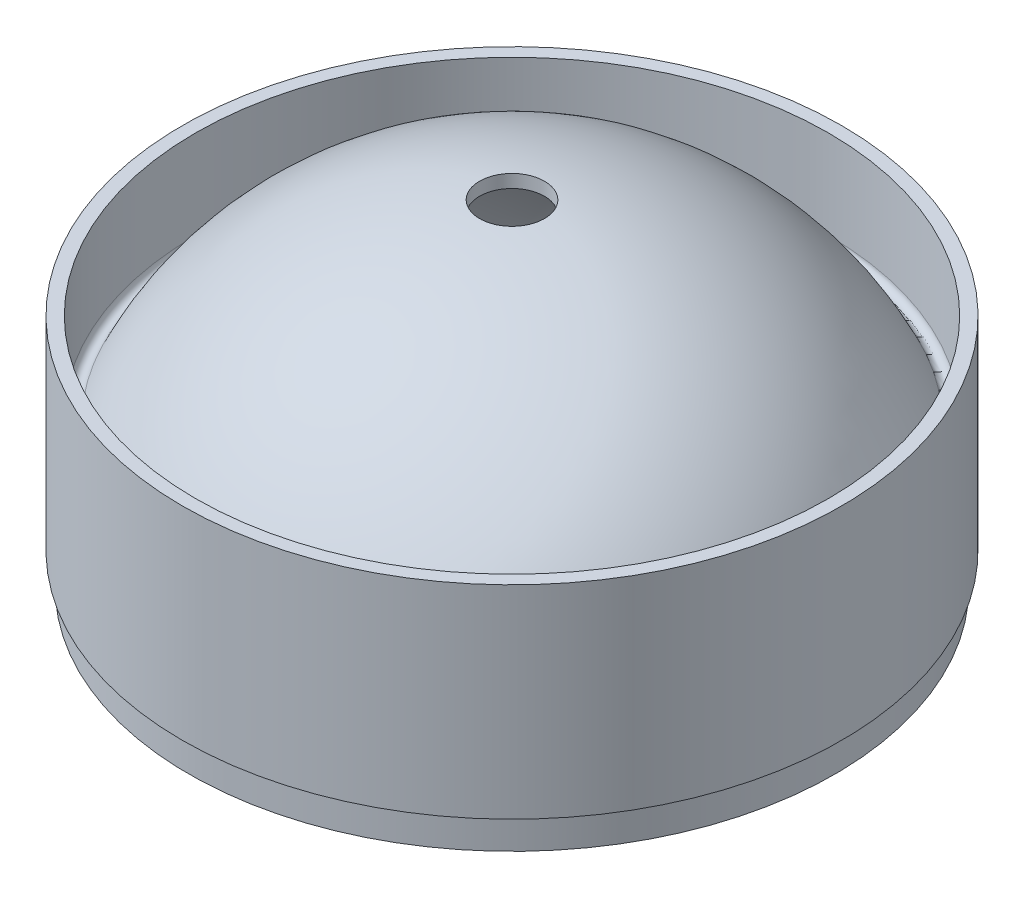
SolidWorks part; units mm, degrees
material "1060 Alloy"
ref_plane "Front Plane" through (0, 0, 0) normal (0, 0, 1) x (1, 0, 0)
ref_plane "Top Plane" through (0, 0, 0) normal (0, 1, 0) x (1, 0, 0)
ref_plane "Right Plane" through (0, 0, 0) normal (1, 0, 0) x (0, 0, -1)
sketch "Sketch2" plane through (0, 0, 0) normal (0, 0, 1) x (1, 0, 0)
  line L0 (0, 0) -> (0, 1000) construction
  line L1 (0, 900) -> (127, 900) construction
  line L2 (127, 900) -> (127, 965.7303)
  line L4 (122, 965.7303) -> (122, 931.4606)
  line L5 (122, 900) -> (122, 875)
  line L6 (127, 900) -> (127, 887.5)
  line L7 (122, 875) -> (124.5, 875)
  line L8 (127, 887.5) -> (124.5, 887.5)
  line L9 (124.5, 887.5) -> (124.5, 875)
  line L10 (0, 1005) -> (0, 1000)
  line L11 (122, 965.7303) -> (127, 965.7303)
  arc A0 (0, 1000) -> (122, 900) centre (0, 875.58) cw
  arc A1 (0, 1005) -> (117.2354, 930.4016) centre (0, 875.58) cw
  arc A2 (0, 1005) -> (126.9027, 900.9814) centre (0, 875.58) cw construction
  arc A3 (122, 931.4606) -> (117.2354, 930.4016) centre (119.5, 931.4606) cw
  point P15 (122, 918.7719)
  point P16 (122, 887.5)
  dimension "D9" = 2.5
  dimension "D1" = 1000
  dimension "D2" = 127
  dimension "D3" = 100
  dimension "D6" = 122
  dimension "D10" = 25
  dimension "D11" = 2.5
  dimension "D13" = 12.5
  dimension "D7" = 5
revolve "Revolve1" add sketch "Sketch2" angle 360 about L0
sketch "Sketch3" plane through (0, 875, 0) normal (0, -1, 0) x (1, 0, 0)
  circle A0 centre (0, 0) radius 12.5
  dimension "D1" = 25
extrude "Cut-Extrude1" cut sketch "Sketch3" against normal blind 1000
